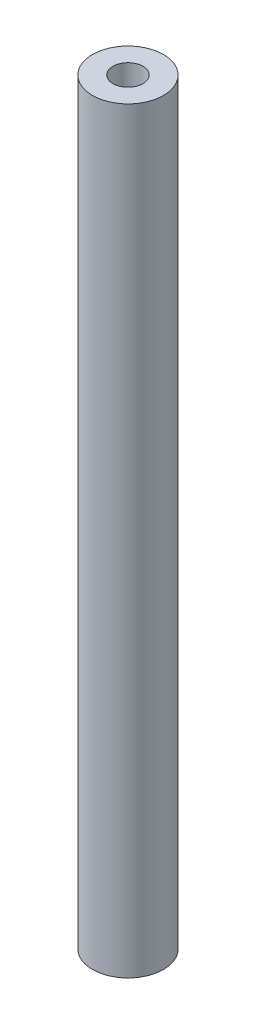
SolidWorks part; units mm, degrees
material "6061-T6 (SS)"
ref_plane "Front Plane" through (0, 0, 0) normal (0, 0, 1) x (1, 0, 0)
ref_plane "Top Plane" through (0, 0, 0) normal (0, 1, 0) x (1, 0, 0)
ref_plane "Right Plane" through (0, 0, 0) normal (1, 0, 0) x (0, 0, -1)
sketch "Sketch1" plane through (0, 0, 0) normal (0, 1, 0) x (1, 0, 0)
  circle A1 centre (0, 0) radius 4.7625
  dimension "D2" = 9.525
extrude "Boss-Extrude1" add sketch "Sketch1" along normal mid plane 101.6
hole_wizard "#10-32 Tapped Hole1" positions "3DSketch1" profile "Sketch2" tap size "#10-32" standard "ANSI Inch"
sketch3d "3DSketch1"
  line L0 (0, 50.8, 0) -> (0, -50.8, 0) construction
  point P0 (0, 50.8, 0)
  point P4 (0, -50.8, 0)
sketch "Sketch2" plane through (0, 50.8, 0) normal (1, 0, 0) x (0, 0, 1)
  line L0 (0, 0) -> (0, 13.1513)
  line L1 (0, 13.1513) -> (2.0193, 11.938)
  line L2 (2.0193, 11.938) -> (2.0193, 0)
  line L5 (2.0193, 0) -> (0, 0)
  line L10 (0, 13.1513) -> (-2.0193, 11.938) construction
  line L11 (0, -6.35) -> (0, 107.95) construction
  dimension "Tap Drill Dia." = 4.0386
  dimension "Tap Drill Depth" = 11.938
  dimension "Drill Angle" = 118
cosmetic thread "Hole Thread1"
cosmetic thread "Hole Thread2"
